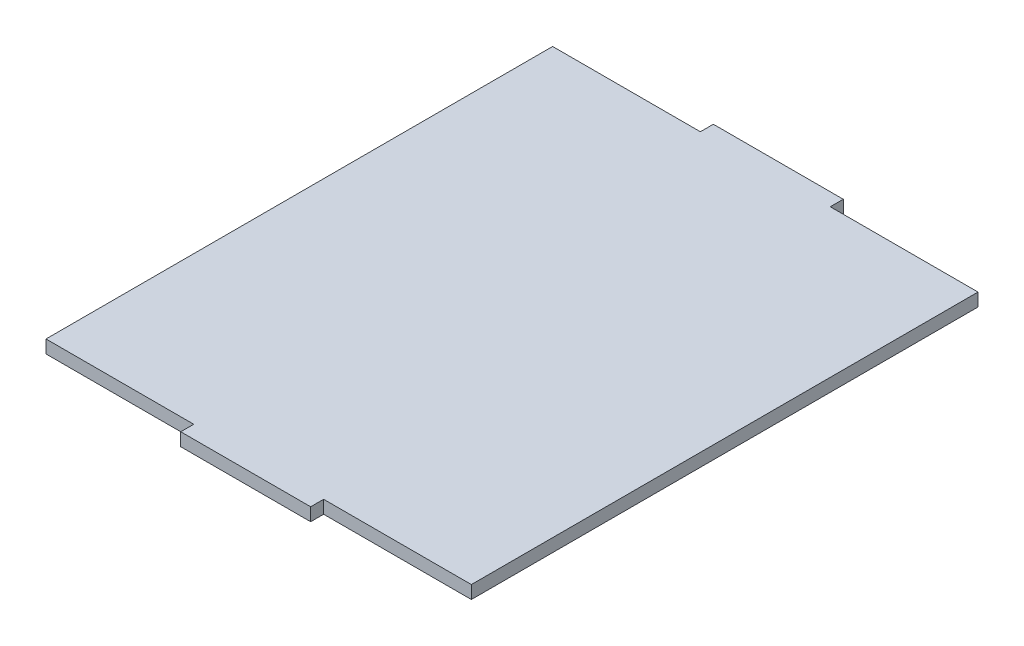
SolidWorks part; units mm, degrees
ref_plane "Front Plane" through (0, 0, 0) normal (0, 0, 1) x (1, 0, 0)
ref_plane "Top Plane" through (0, 0, 0) normal (0, 1, 0) x (1, 0, 0)
ref_plane "Right Plane" through (0, 0, 0) normal (1, 0, 0) x (0, 0, -1)
sketch "Sketch1" plane through (0, 0, 0) normal (0, 1, 0) x (1, 0, 0)
  line L0 (-60.5024, 79.3083) -> (37.7276, 79.3083) construction
  line L1 (-60.5024, 76.3083) -> (-26.3874, 76.3083)
  line L2 (-60.5024, 76.3083) -> (-60.5024, -40.6917)
  line L3 (-60.5024, -40.6917) -> (-26.3874, -40.6917)
  line L4 (37.7276, 76.3083) -> (37.7276, -40.6917)
  line L8 (-11.3874, 79.3083) -> (-11.3874, 76.3083) construction
  line L9 (-11.3874, -40.6917) -> (-11.3874, -43.6917) construction
  line L17 (-26.3874, 79.3083) -> (-26.3874, 76.3083)
  line L19 (3.6126, 79.3083) -> (3.6126, 76.3083)
  line L20 (-26.3874, -40.6917) -> (-26.3874, -43.6917)
  line L21 (3.6126, -40.6917) -> (3.6126, -43.6917)
  line L22 (-26.3874, -43.6917) -> (3.6126, -43.6917)
  line L23 (-26.3874, 79.3083) -> (3.6126, 79.3083)
  line L24 (3.6126, 76.3083) -> (37.7276, 76.3083)
  line L25 (3.6126, -40.6917) -> (37.7276, -40.6917)
  line L26 (-60.5024, 76.3083) -> (37.7276, 76.3083) construction
  line L27 (-11.3874, 76.3083) -> (-11.3874, -40.6917) construction
  point P4 (-11.3874, 17.8083)
  point P30 (-11.3874, 28.7205)
  point P62 (-11.3874, 17.8083)
  dimension "D7" = 98.23
  dimension "D9" = 117
  dimension "D10" = 3
  dimension "D2" = 3
  dimension "D3" = 15
  dimension "D4" = 15
  dimension "D5" = 15
  dimension "D6" = 15
extrude "Boss-Extrude1" add sketch "Sketch1" along normal blind 3
